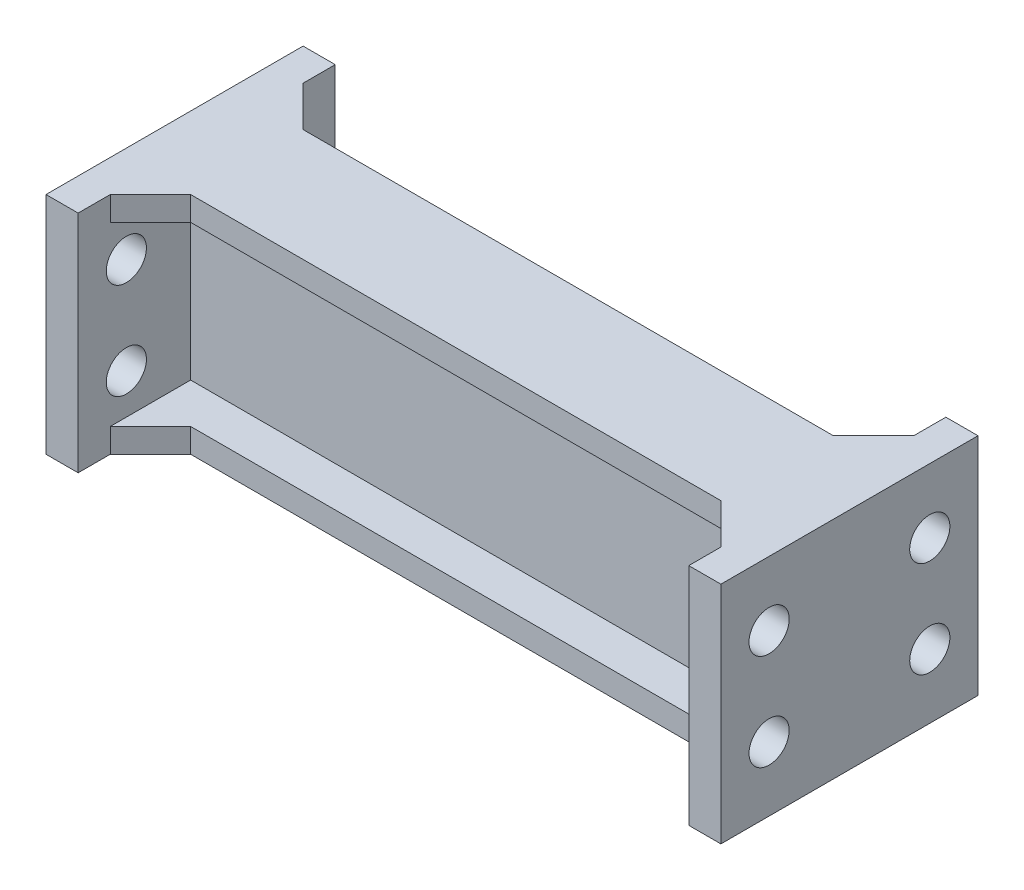
SolidWorks part; units mm, degrees
ref_plane "Front Plane" through (0, 0, 0) normal (0, 0, 1) x (1, 0, 0)
ref_plane "Top Plane" through (0, 0, 0) normal (0, 1, 0) x (1, 0, 0)
ref_plane "Right Plane" through (0, 0, 0) normal (1, 0, 0) x (0, 0, -1)
sketch "Sketch1" plane through (0, 0, 0) normal (0, 1, 0) x (1, 0, 0)
  line L0 (-21, 0) -> (21, 0) construction
  line L1 (-19, 1) -> (19, 1)
  line L2 (-21, 1) -> (-21, -1)
  line L3 (-19, -1) -> (19, -1)
  line L4 (21, 1) -> (21, -1)
  line L5 (-21, 1) -> (21, -1) construction
  line L6 (-21, -1) -> (21, 1) construction
  line L7 (21, 1) -> (21, 8)
  line L8 (19, 1) -> (19, 8)
  line L9 (19, 8) -> (21, 8)
  line L10 (21, -1) -> (21, -8)
  line L11 (19, -8) -> (21, -8)
  line L12 (19, -1) -> (19, -8)
  line L13 (0, 0) -> (0, 1) construction
  line L14 (0, 1) -> (0, -1) construction
  line L15 (-19, -8) -> (-21, -8)
  line L16 (-21, -1) -> (-21, -8)
  line L17 (-19, -1) -> (-19, -8)
  line L18 (-21, 1) -> (-21, 8)
  line L19 (-19, 8) -> (-21, 8)
  line L20 (-19, 1) -> (-19, 8)
  point P0 (0, 0)
  dimension "D1" = 2
  dimension "D2" = 42
  dimension "D3" = 7
  dimension "D4" = 2
extrude "Boss-Extrude1" add sketch "Sketch1" along normal blind 14
sketch "Sketch2" plane through (21, 0, 0) normal (1, 0, 0) x (0, 0, -1)
  line L0 (0, 14) -> (0, 0) construction
  line L1 (-8, 14) -> (8, 14) construction
  line L2 (-8, 7) -> (8, 7) construction
  line L3 (-8, 14) -> (-8, 0) construction
  line L4 (8, 14) -> (8, 0) construction
  circle A0 centre (5, 10) radius 1.25
  circle A1 centre (5, 4) radius 1.25
  circle A2 centre (-5, 4) radius 1.25
  circle A3 centre (-5, 10) radius 1.25
  dimension "D1" = 2.5
  dimension "D2" = 5
  dimension "D3" = 3
extrude "Cut-Extrude1" cut sketch "Sketch2" against normal through all
sketch "Sketch3" plane through (0, 14, 0) normal (0, 1, 0) x (1, 0, 0)
  line L0 (-19, 1) -> (-19, 6)
  line L1 (-19, 1) -> (-19, 8) construction
  line L2 (-19, 1) -> (-14, 1)
  line L3 (19, 1) -> (-19, 1) construction
  line L4 (-19, 6) -> (-16.5, 3.5)
  line L5 (-21, 0) -> (21, 0) construction
  line L6 (-21, 8) -> (-21, -8) construction
  line L7 (21, -8) -> (21, 8) construction
  line L8 (0, 1) -> (0, -1) construction
  line L9 (-19, -1) -> (19, -1) construction
  line L10 (19, 1) -> (19, 6)
  line L11 (19, 1) -> (14, 1)
  line L12 (19, 6) -> (16.5, 3.5)
  line L13 (19, -1) -> (14, -1)
  line L14 (19, -6) -> (16.5, -3.5)
  line L15 (19, -1) -> (19, -6)
  line L16 (-19, -1) -> (-19, -6)
  line L17 (-19, -1) -> (-14, -1)
  line L18 (-19, -6) -> (-16.5, -3.5)
  line L19 (-16.5, 3.5) -> (16.5, 3.5)
  line L20 (-14, 1) -> (14, 1)
  line L21 (-16.5, -3.5) -> (16.5, -3.5)
  line L22 (-14, -1) -> (14, -1)
  dimension "D1" = 5
  dimension "D2" = 5
extrude "Boss-Extrude2" add sketch "Sketch3" against normal blind 1.5
ref_plane "Plane1" through (0, 7, 0) normal (0, 1, 0) x (1, 0, 0)
mirror "Mirror1" about plane through (0, 7, 0) normal (0, 1, 0) of "Boss-Extrude2"
